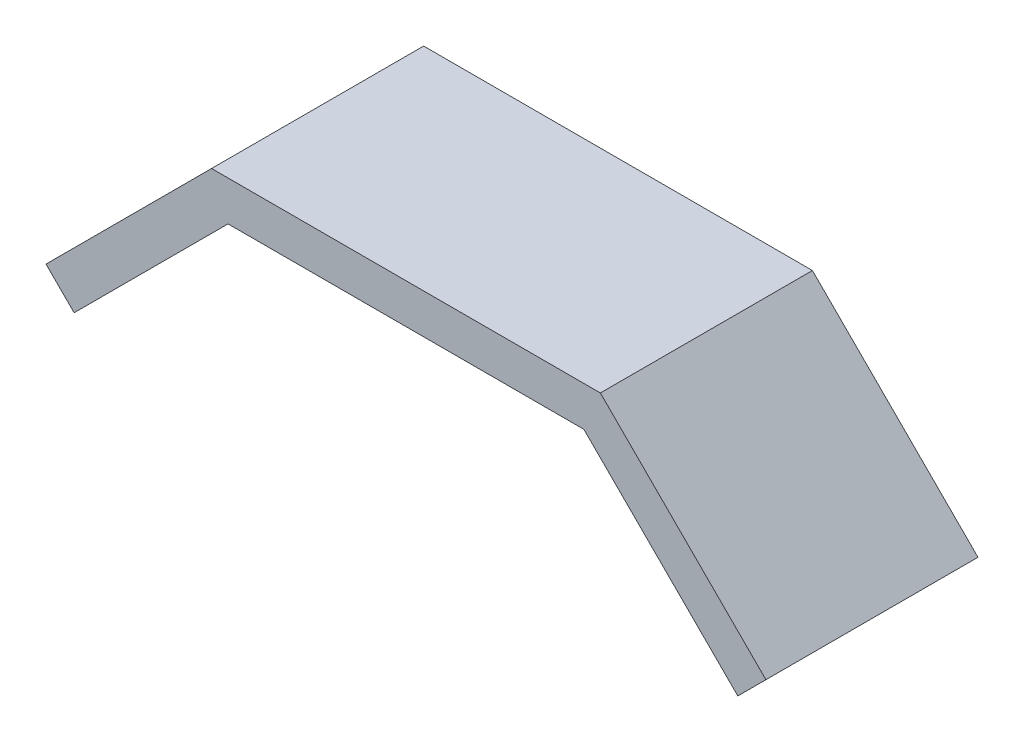
SolidWorks part; units mm, degrees
ref_plane "Front Plane" through (0, 0, 0) normal (0, 0, 1) x (1, 0, 0)
ref_plane "Top Plane" through (0, 0, 0) normal (0, 1, 0) x (1, 0, 0)
ref_plane "Right Plane" through (0, 0, 0) normal (1, 0, 0) x (0, 0, -1)
sketch "Sketch1" plane through (0, 0, 0) normal (0, 0, 1) x (1, 0, 0)
  line L0 (-128.7029, 0) -> (159.8326, 0) construction
  line L1 (0, 103.2636) -> (0, -134.0586) construction
  line L2 (-81.4767, -37.4767) -> (-44, 0)
  line L3 (-44, 0) -> (44, 0)
  line L4 (44, 0) -> (81.4767, -37.4767)
  dimension "D1" = 88
  dimension "D2" = 44
  dimension "D3" = 45
  dimension "D4" = 45
  dimension "D5" = 53
  dimension "D6" = 53
extrude "Extrude-Thin1" add sketch "Sketch1" along normal mid plane 48 thin
sketch "Sketch2" plane through (22, 22, 0) normal (0.7071, 0.7071, 0) x (0, 0, -1)
  line L0 (-57.6151, -11.4203) -> (73.6916, -11.4203) construction
  line L1 (0, 81.8614) -> (0, -195.3806) construction
  line L2 (66.0362, -57.1127) -> (-59.8767, -57.1127) construction
  line L3 (-24, -84.1127) -> (24, -84.1127) construction
  line L5 (-7, -56.7596) -> (7, -56.7596)
  line L6 (-7, -56.7596) -> (-7, -84.1127)
  line L7 (-7, -84.1127) -> (7, -84.1127)
  line L8 (7, -56.7596) -> (7, -84.1127)
  circle A0 centre (0, -56.7596) radius 7
  dimension "D2" = 14
  dimension "D1" = 27
ref_plane "Plane1" through (81.4767, -37.4767, -24) normal (-0.7071, -0.7071, 0) x (0, 0, 1)
